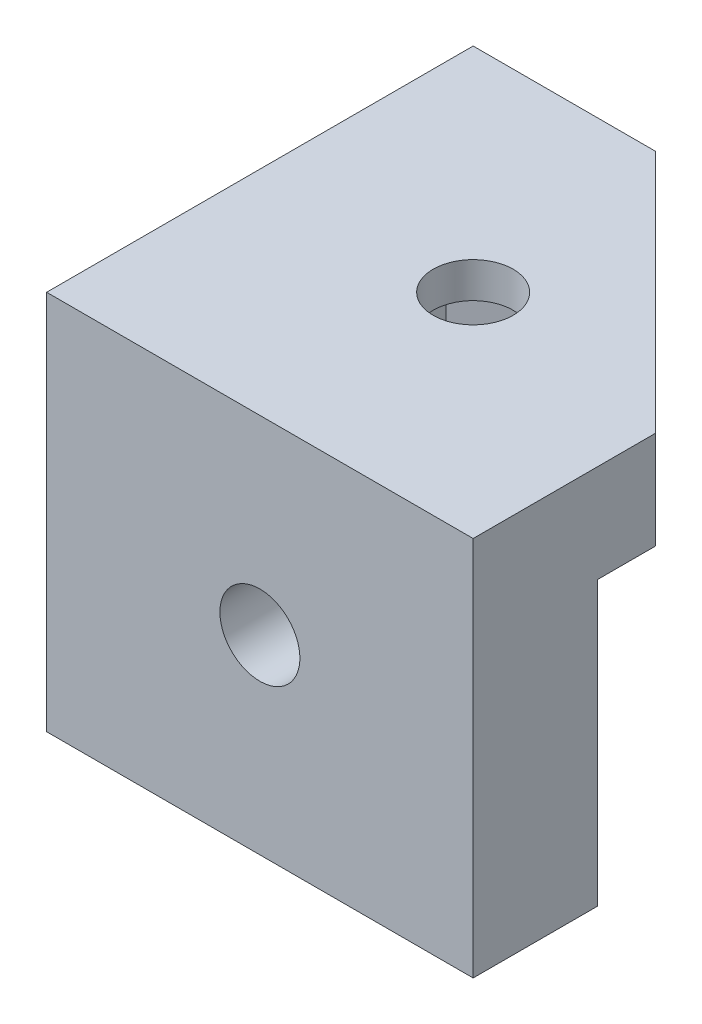
SolidWorks part; units mm, degrees
ref_plane "Front Plane" through (0, 0, 0) normal (0, 0, 1) x (1, 0, 0)
ref_plane "Top Plane" through (0, 0, 0) normal (0, 1, 0) x (1, 0, 0)
ref_plane "Right Plane" through (0, 0, 0) normal (1, 0, 0) x (0, 0, -1)
sketch "Sketch1" plane through (0, 0, 0) normal (0, 1, 0) x (1, 0, 0)
  line L1 (0, 0) -> (38.1, 0)
  line L5 (0, 0) -> (0, 38.1)
  line L6 (0, 38.1) -> (38.1, 38.1)
  line L8 (38.1, 38.1) -> (38.1, 0)
  dimension "D1" = 38.1
extrude "Main Body" add sketch "Sketch1" along normal blind 34
sketch "Sketch3" plane through (0, 0, 0) normal (0, 0, 1) x (1, 0, 0)
  line L0 (0, 0) -> (38.1, 34) construction
  circle A0 centre (19.05, 17) radius 3.5719
  circle A1 centre (19.05, 17) radius 7.9375 construction
  dimension "D1" = 7.1437
  dimension "D2" = 15.875
extrude "9/32 Right Rail" cut sketch "Sketch3" against normal blind 5.5562 and the other way through all
sketch "Sketch4" plane through (0, 0, 0) normal (-1, 0, 0) x (0, 0, 1)
  line L0 (0, 0) -> (-38.1, 34) construction
  circle A0 centre (-19.05, 17) radius 3.5719
  circle A1 centre (-19.05, 17) radius 7.9375 construction
  dimension "D1" = 7.1437
  dimension "D2" = 15.875
extrude "9/32 Left Rail" cut sketch "Sketch4" against normal blind 5.5562
sketch "Sketch8" plane through (0, 34, 0) normal (0, 1, 0) x (1, 0, 0)
  line L0 (0, 0) -> (38.1, 38.1) construction
  circle A0 centre (19.05, 19.05) radius 3.175 construction
  circle A1 centre (19.05, 19.05) radius 7.9375 construction
  circle A2 centre (19.05, 19.05) radius 3.5719
  dimension "D1" = 6.35
  dimension "D2" = 15.875
  dimension "D3" = 0.3969
extrude "9/32 Topper" cut sketch "Sketch8" against normal blind 10 and the other way through all
ref_plane "Plane1" through (5.5562, 0, 0) normal (-1, 0, 0) x (0, 0, 1)
sketch "Sketch9" plane through (0, 0, 0) normal (-1, 0, 0) x (0, 0, 1)
  line L0 (-19.05, 0) -> (-19.05, 34) construction
  line L1 (-12.6342, 17) -> (-15.8421, 22.5562) construction
  line L2 (-15.8421, 22.5562) -> (-22.2579, 22.5562) construction
  line L3 (-22.2579, 22.5562) -> (-25.4658, 17) construction
  line L4 (-25.4658, 17) -> (-22.2579, 11.4437) construction
  line L5 (-22.2579, 11.4437) -> (-15.8421, 11.4437) construction
  line L6 (-15.8421, 11.4437) -> (-12.6342, 17) construction
  line L7 (-38.1, 0) -> (0, 0) construction
  line L8 (-38.1, 34) -> (0, 34) construction
  line L9 (-22.3725, 22.7547) -> (-25.6949, 17)
  line L10 (-25.6949, 17) -> (-22.3725, 11.2453)
  line L11 (-22.3725, 11.2453) -> (-15.7275, 11.2453)
  line L12 (-15.7275, 11.2453) -> (-12.4051, 17)
  line L13 (-12.4051, 17) -> (-15.7275, 22.7547)
  line L14 (-15.7275, 22.7547) -> (-22.3725, 22.7547)
  line L15 (-38.1, 27.65) -> (-38.1, 6.35) construction
  line L16 (-38.1, 34) -> (-38.1, 0) construction
  line L17 (-38.1, 6.35) -> (-5.5562, 6.35) construction
  line L18 (-5.5562, 6.35) -> (-5.5562, 27.65) construction
  line L19 (-5.5562, 27.65) -> (-38.1, 27.65) construction
  line L20 (0, 34) -> (0, 0) construction
  circle A0 centre (-19.05, 17) radius 5.5563 construction
  point P15 (-19.05, 17)
  point P27 (-38.1, 17)
  point P29 (-38.1, 17)
  dimension "D1" = 11.1125
  dimension "D3" = 5.5562
  dimension "D4" = 6.35
  dimension "D2" = 0.1984
extrude "Hex Hole Right" cut sketch "Sketch9" against normal up to surface (32.5438 mm away) from surface at -5.5563 up to face at (38.1, 17, -19.05) starting at plane "Plane1"
ref_plane "Plane2" through (0, 0, -5.5563) normal (0, 0, 1) x (1, 0, 0)
sketch "Sketch10" plane through (0, 0, 0) normal (0, 0, 1) x (1, 0, 0)
  line L0 (19.05, 0) -> (19.05, 34) construction
  line L1 (0, 0) -> (38.1, 0) construction
  line L2 (0, 34) -> (38.1, 34) construction
  line L3 (15.7275, 22.7547) -> (12.4051, 17)
  line L4 (25.4658, 17) -> (22.2579, 22.5562) construction
  line L5 (22.2579, 22.5562) -> (15.8421, 22.5562) construction
  line L6 (15.8421, 22.5562) -> (12.6342, 17) construction
  line L13 (12.6342, 17) -> (15.8421, 11.4437) construction
  line L14 (15.8421, 11.4437) -> (22.2579, 11.4437) construction
  line L15 (22.2579, 11.4437) -> (25.4658, 17) construction
  line L16 (12.4051, 17) -> (15.7275, 11.2453)
  line L17 (15.7275, 11.2453) -> (22.3725, 11.2453)
  line L18 (22.3725, 11.2453) -> (25.6949, 17)
  line L19 (25.6949, 17) -> (22.3725, 22.7547)
  line L20 (22.3725, 22.7547) -> (15.7275, 22.7547)
  circle A0 centre (19.05, 17) radius 5.5563 construction
  dimension "D1" = 11.1125
  dimension "D2" = 0.1984
extrude "Hex Hole Left" cut sketch "Sketch10" against normal up to surface (32.5438 mm away) from surface at -5.5563 up to face at (19.05, 17, -38.1) starting at plane "Plane2"
sketch "Sketch13" plane through (0, 34, 0) normal (0, 1, 0) x (1, 0, 0)
  line L0 (22.3725, 5.5563) -> (15.7275, 5.5563) construction
  line L1 (5.5562, 15.7275) -> (5.5562, 22.3725) construction
  line L2 (38.1, 11.1125) -> (11.1125, 11.1125)
  line L3 (11.1125, 38.1) -> (11.1125, 11.1125)
  line L5 (22.3725, 5.5563) -> (15.7275, 5.5563) construction
  line L6 (5.5562, 15.7275) -> (5.5562, 22.3725) construction
  line L7 (38.1, 38.1) -> (0, 38.1) construction
  line L8 (38.1, 0) -> (38.1, 38.1) construction
  line L9 (11.1125, 38.1) -> (38.1, 38.1)
  line L10 (38.1, 38.1) -> (38.1, 11.1125)
  point P2 (8.9807, 8.9807)
  point P3 (13.3137, 13.3137)
  point P15 (10.6863, 10.6863)
  dimension "D1" = 5.5562
ref_plane "Plane4" through (0, 17, 0) normal (0, 1, 0) x (1, 0, 0)
extrude "Inner Cavity" cut sketch "Sketch13" along direction (0, -1, 0) on the side of the normal offset from surface 8.7312 and the other way up to surface (22.7547 mm away) from surface at -17.4625
sketch "Sketch14" plane through (0, 34, 0) normal (0, 1, 0) x (1, 0, 0)
  line L0 (38.1, 0) -> (0, 38.1) construction
  line L1 (24.8047, 22.3725) -> (19.05, 25.6949)
  line L2 (24.6063, 22.2579) -> (19.05, 25.4658) construction
  line L3 (19.05, 25.4658) -> (13.4938, 22.2579) construction
  line L4 (13.4938, 22.2579) -> (13.4938, 15.8421) construction
  line L5 (13.4938, 15.8421) -> (19.05, 12.6342) construction
  line L6 (19.05, 12.6342) -> (24.6063, 15.8421) construction
  line L7 (24.6063, 15.8421) -> (24.6063, 22.2579) construction
  line L8 (19.05, 25.6949) -> (13.2953, 22.3725)
  line L9 (13.2953, 22.3725) -> (13.2953, 15.7275)
  line L10 (13.2953, 15.7275) -> (19.05, 12.4051)
  line L11 (19.05, 12.4051) -> (24.8047, 15.7275)
  line L12 (24.8047, 15.7275) -> (24.8047, 22.3725)
  line L14 (38.1, 38.1) -> (38.1, 11.1125) construction
  circle A0 centre (19.05, 19.05) radius 5.5562 construction
  point P18 (0, 0)
  dimension "D1" = 11.1125
  dimension "D2" = 0.1984
extrude "Hex Hole Top" cut sketch "Sketch14" along normal offset from surface (13.825 mm away) 3.175 from surface at -17 up to face at (19.05, 34, -22.6219) starting at plane "Plane4"
sketch "Sketch16" plane through (0, 34, 0) normal (0, 1, 0) x (1, 0, 0)
  line L0 (38.1, 38.1) -> (16.2767, 38.1)
  line L1 (38.1, 38.1) -> (0, 38.1) construction
  line L2 (16.2767, 38.1) -> (38.1, 16.2767)
  line L3 (38.1, 16.2767) -> (38.1, 38.1)
  line L4 (38.1, 0) -> (38.1, 38.1) construction
  circle A2 centre (19.05, 19.05) radius 3.5719 construction
  dimension "D1" = 7.9375
extrude "Top Corner" cut sketch "Sketch16" against normal up to next
